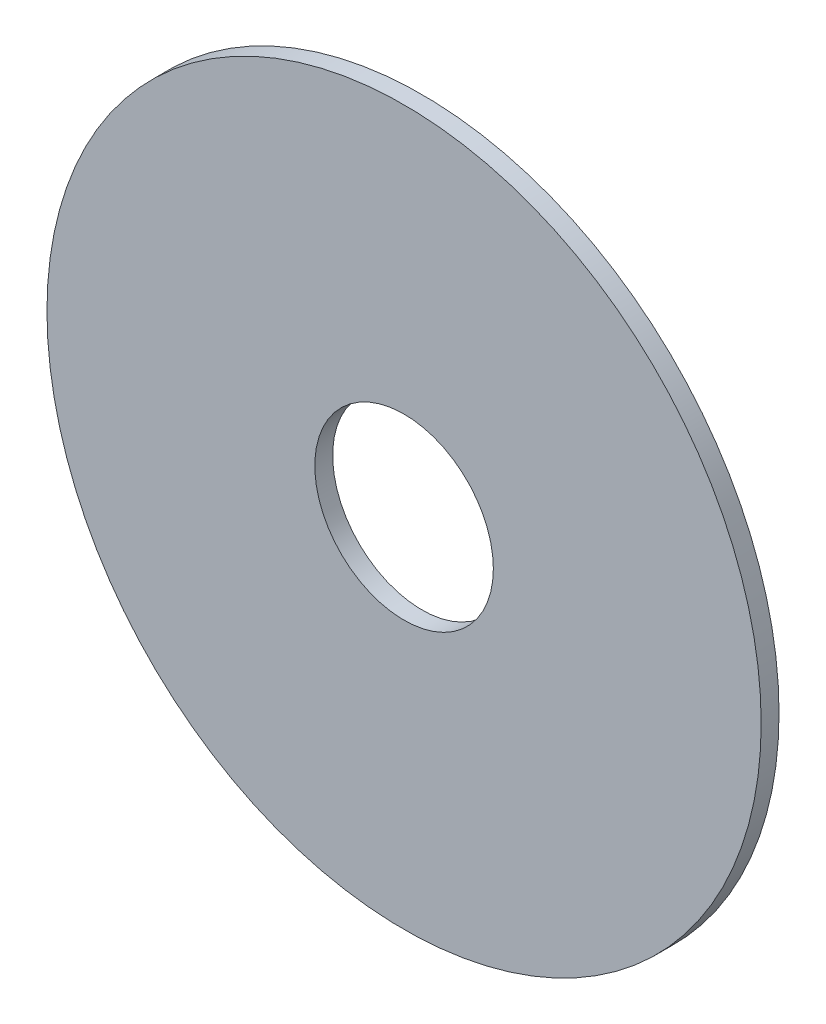
SolidWorks part; units mm, degrees
ref_plane "Front Plane" through (0, 0, 0) normal (0, 0, 1) x (1, 0, 0)
ref_plane "Top Plane" through (0, 0, 0) normal (0, 1, 0) x (1, 0, 0)
ref_plane "Right Plane" through (0, 0, 0) normal (1, 0, 0) x (0, 0, -1)
sketch "Sketch1" plane through (0, 0, 0) normal (0, 0, 1) x (1, 0, 0)
  circle A0 centre (0, 0) radius 20
extrude "Boss-Extrude1" add sketch "Sketch1" along normal blind 1
sketch "Sketch2" plane through (0, 0, 1) normal (0, 0, 1) x (1, 0, 0)
  circle A0 centre (0, 0) radius 5
extrude "Cut-Extrude1" cut sketch "Sketch2" against normal blind 4
